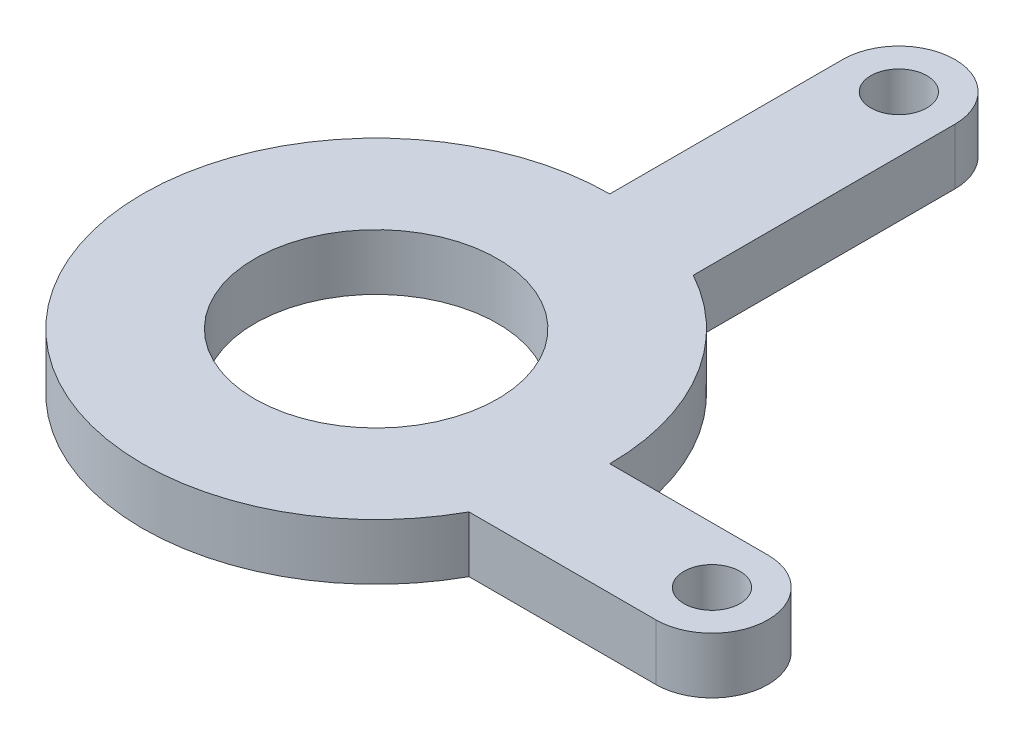
SolidWorks part; units mm, degrees
ref_plane "Front Plane" through (0, 0, 0) normal (0, 0, 1) x (1, 0, 0)
ref_plane "Top Plane" through (0, 0, 0) normal (0, 1, 0) x (1, 0, 0)
ref_plane "Right Plane" through (0, 0, 0) normal (1, 0, 0) x (0, 0, -1)
sketch "Sketch1" plane through (0, 0, 0) normal (0, 1, 0) x (1, 0, 0)
  line L0 (0, 12.5) -> (0, -12.5) construction
  line L1 (-12.5, 0) -> (12.5, 0) construction
  line L2 (0, 0) -> (-8.8388, 8.8388) construction
  line L3 (0, 0) -> (8.8388, 8.8388) construction
  line L6 (0, 12.5) -> (0, 24.9659)
  line L8 (6, 10.9659) -> (6, 24.9659)
  line L9 (12.5, 0) -> (20.9659, 0)
  line L11 (10.9659, -6) -> (20.9659, -6)
  arc A0 (0, 12.5) -> (10.9659, -6) centre (0, 0) ccw
  circle A1 centre (0, 0) radius 6.5
  arc A2 (6, 24.9659) -> (0, 24.9659) centre (3, 24.9659) ccw
  circle A3 centre (3, 24.9659) radius 1.5
  arc A4 (20.9659, -6) -> (20.9659, 0) centre (20.9659, -3) ccw
  arc A5 (12.5, 0) -> (6, 10.9659) centre (0, 0) ccw
  circle A6 centre (20.9659, -3) radius 1.5
  dimension "D1" = 25
  dimension "D2" = 13
  dimension "D5" = 6
  dimension "D6" = 3
  dimension "D9" = 6
  dimension "D10" = 3
  dimension "D3" = 6
  dimension "D4" = 14
  dimension "D7" = 6
  dimension "D8" = 10
extrude "Boss-Extrude1" add sketch "Sketch1" along normal blind 3 contours A1 | A0 L11 A4 L9 A5 L8 A2 L6 | A6 | A3
